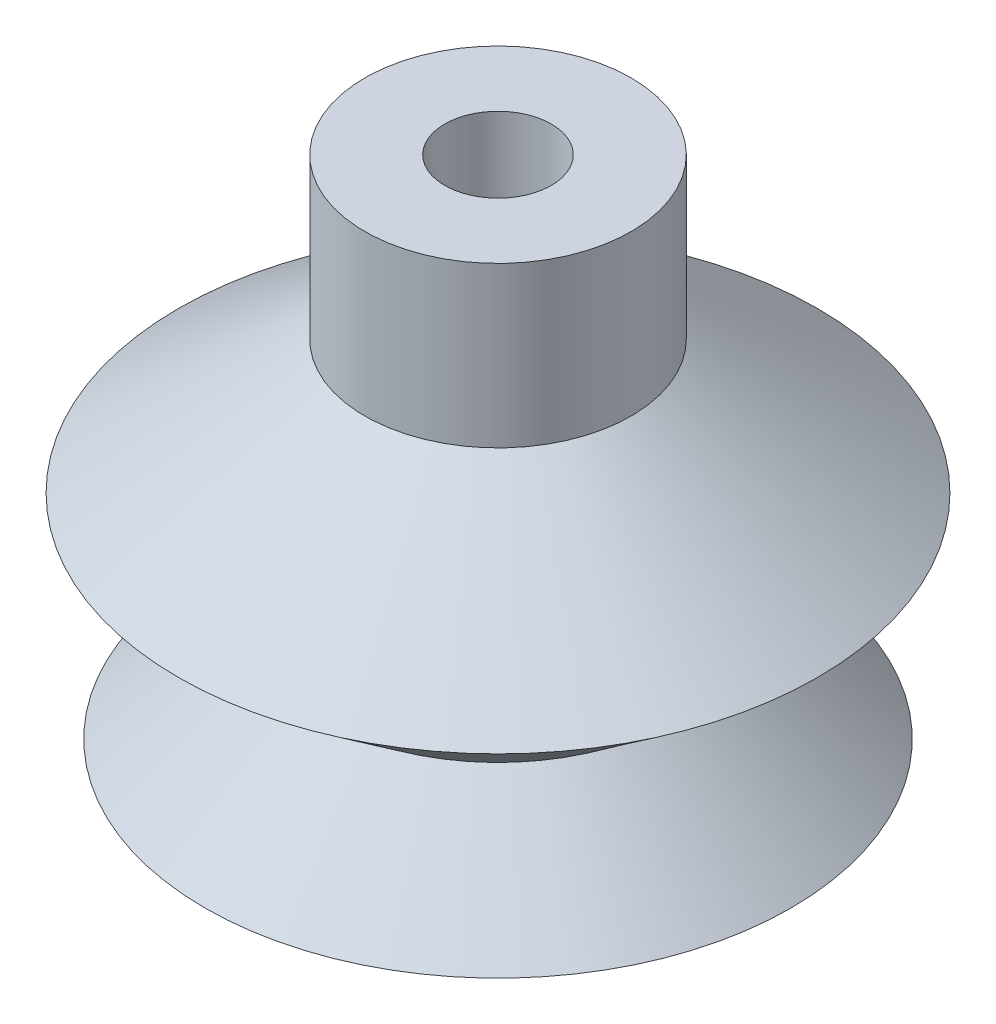
SolidWorks part; units mm, degrees
ref_plane "Face" through (0, 0, 0) normal (0, 0, 1) x (1, 0, 0)
ref_plane "Dessus" through (0, 0, 0) normal (0, 1, 0) x (1, 0, 0)
ref_plane "Droite" through (0, 0, 0) normal (1, 0, 0) x (0, 0, -1)
sketch "Esquisse1" plane through (0, 0, 0) normal (0, 0, 1) x (1, 0, 0)
  line L0 (0, 0) -> (0, 19) construction
  line L1 (5, 19) -> (5, 13)
  line L2 (0, 19) -> (5, 19) construction
  line L3 (0, 0) -> (12, 0) construction
  line L4 (12, 0) -> (12, 19) construction
  line L5 (12, 19) -> (5, 19) construction
  line L6 (2, 10) -> (3.6886, 10)
  line L7 (3.6886, 10) -> (10, 8)
  line L8 (5, 13) -> (12, 8)
  line L9 (10, 8) -> (5.2775, 4)
  line L10 (5.2775, 4) -> (9.5389, 0)
  line L11 (2, 10) -> (2, 19)
  line L12 (5, 19) -> (2, 19)
  line L13 (6.7386, 4) -> (11, 0)
  line L14 (11, 0) -> (9.5389, 0)
  line L16 (6.7386, 4) -> (12, 8)
  line L17 (5.2775, 4) -> (6.7386, 4) construction
  line L18 (10, 8) -> (12, 8) construction
  dimension "D1" = 2
  dimension "D2" = 5
  dimension "D3" = 12
  dimension "D4" = 11
  dimension "D5" = 8
  dimension "D6" = 1
  dimension "D7" = 9
  dimension "D8" = 19
  dimension "D9" = 2
  dimension "D10" = 4
  dimension "D11" = 6
revolve "Révolution1" add sketch "Esquisse1" angle 360 about L0
